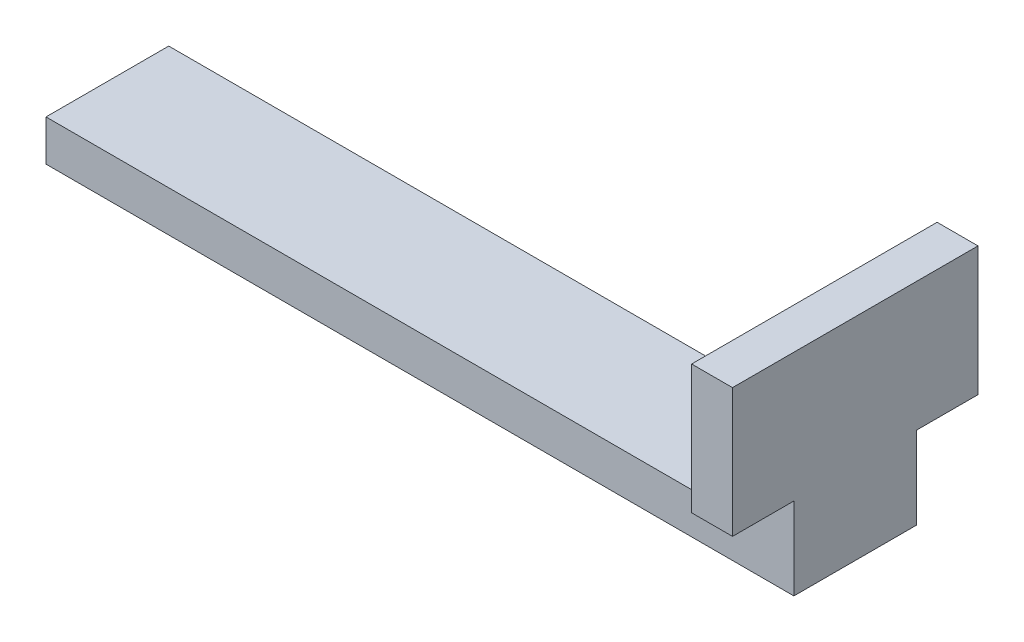
SolidWorks part; units mm, degrees
ref_plane "Front Plane" through (0, 0, 0) normal (0, 0, 1) x (1, 0, 0)
ref_plane "Top Plane" through (0, 0, 0) normal (0, 1, 0) x (1, 0, 0)
ref_plane "Right Plane" through (0, 0, 0) normal (1, 0, 0) x (0, 0, -1)
sketch "Sketch2" plane through (0, 0, 0) normal (0, 0, 1) x (1, 0, 0)
  line L1 (-109.728, 0) -> (0, 0)
  line L2 (-109.728, 0) -> (-109.728, 6.35)
  line L3 (-109.728, 6.35) -> (0, 6.35)
  line L5 (0, 0) -> (6.35, 0)
  line L6 (0, 6.35) -> (0, 32.766)
  line L7 (0, 32.766) -> (6.35, 32.766)
  line L8 (6.35, 0) -> (6.35, 32.766)
  dimension "D1" = 6.35
  dimension "D2" = 32.766
  dimension "D3" = 116.078
extrude "Boss-Extrude1" add sketch "Sketch2" along normal mid plane 19.05
sketch "Sketch3" plane through (0, 0, 0) normal (-1, 0, 0) x (0, 0, 1)
  line L0 (9.525, 32.766) -> (-9.525, 32.766) construction
  line L1 (-19.05, 32.766) -> (19.05, 32.766)
  line L2 (-19.05, 32.766) -> (-19.05, 12.766)
  line L3 (-19.05, 12.766) -> (19.05, 12.766)
  line L4 (19.05, 32.766) -> (19.05, 12.766)
  point P6 (0, 32.766)
  dimension "D1" = 20
  dimension "D2" = 38.1
extrude "Boss-Extrude2" add sketch "Sketch3" against normal up to surface (6.35 mm away) up to face at (6.35, 16.383, 0)
